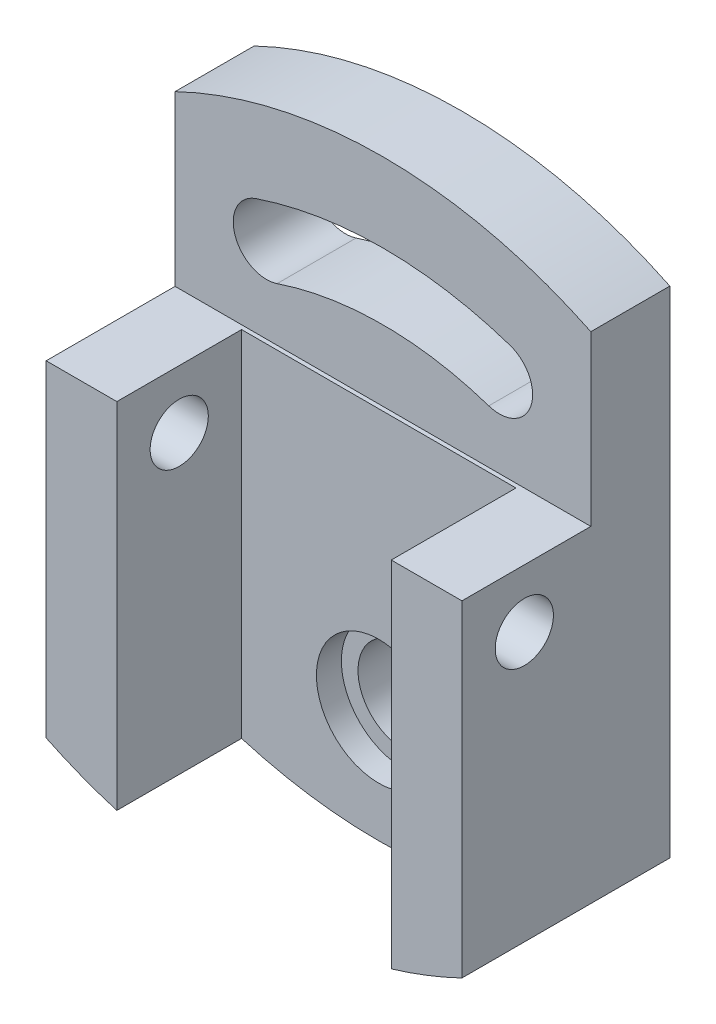
SolidWorks part; units mm, degrees
ref_plane "Front Plane" through (0, 0, 0) normal (0, 0, 1) x (1, 0, 0)
ref_plane "Top Plane" through (0, 0, 0) normal (0, 1, 0) x (1, 0, 0)
ref_plane "Right Plane" through (0, 0, 0) normal (1, 0, 0) x (0, 0, -1)
sketch "Sketch3" plane through (0, 0, 0) normal (0, 0, 1) x (1, 0, 0)
  line L0 (0, 0) -> (0, -134.0527) construction
  line L2 (-50, 103.5616) -> (-50, -15.5616)
  line L4 (50, 103.5616) -> (50, -15.5616)
  arc A0 (-50, 103.5616) -> (50, 103.5616) centre (0, 0) cw
  arc A1 (-28, 83.4266) -> (28, 83.4266) centre (0, 0) cw construction
  arc A3 (30.5455, 91.0109) -> (-30.5455, 91.0109) centre (0, 0) ccw
  arc A8 (25.4545, 75.8424) -> (-25.4545, 75.8424) centre (0, 0) ccw
  arc A9 (25.4545, 75.8424) -> (30.5455, 91.0109) centre (28, 83.4266) ccw
  arc A10 (-30.5455, 91.0109) -> (-25.4545, 75.8424) centre (-28, 83.4266) ccw
  arc A11 (-50, -15.5616) -> (50, -15.5616) centre (0, 88) ccw
  point P8 (0, 115)
  point P9 (0, 88)
  dimension "D1" = 115
  dimension "D2" = 88
  dimension "D4" = 115
  dimension "D6" = 8
  dimension "D5" = 100
  dimension "D7" = 56
extrude "Boss-Extrude1" add sketch "Sketch3" along normal blind 20
sketch "Sketch5" plane through (0, 0, 20) normal (0, 0, 1) x (1, 0, 0)
  line L0 (-50, 63) -> (-33, 63)
  line L1 (50, -15.5616) -> (50, 103.5616) construction
  line L2 (-50, 103.5616) -> (-50, -15.5616) construction
  line L3 (50, -15.5616) -> (50, 63)
  line L4 (-50, 63) -> (-50, -15.5616)
  line L5 (-33, 63) -> (-33, -22.1635)
  line L6 (33, 63) -> (33, -22.1635)
  line L7 (0, 0) -> (0, 28.0508) construction
  line L8 (33, 63) -> (50, 63)
  arc A0 (-50, -15.5616) -> (50, -15.5616) centre (0, 88) ccw construction
  arc A1 (-50, -15.5616) -> (-33, -22.1635) centre (0, 88) ccw
  arc A2 (33, -22.1635) -> (50, -15.5616) centre (0, 88) ccw
  point P5 (0, -27)
  dimension "D1" = 90
  dimension "D2" = 66
extrude "Boss-Extrude2" add sketch "Sketch5" along normal blind 30
sketch "Sketch6" plane through (0, 0, 20) normal (0, 0, 1) x (1, 0, 0)
  line L0 (-33, 63) -> (33, 63)
  line L6 (-50, 63) -> (-33, 63)
  line L7 (-33, 63) -> (-33, -22.1635)
  line L8 (33, -22.1635) -> (33, 63)
  line L9 (33, 63) -> (50, 63)
  line L10 (50, 63) -> (50, 103.5616)
  line L11 (-50, 103.5616) -> (-50, 63)
  line L12 (-50, 63) -> (-33, 63)
  line L15 (33, 63) -> (50, 63)
  line L16 (50, 63) -> (50, 103.5616)
  line L17 (-50, 103.5616) -> (-50, 63)
  arc A2 (-33, -22.1635) -> (33, -22.1635) centre (0, 88) ccw
  arc A3 (50, 103.5616) -> (-50, 103.5616) centre (0, 0) ccw
  arc A5 (50, 103.5616) -> (-50, 103.5616) centre (0, 0) ccw
  dimension "D1" = 0
extrude "Cut-Extrude1" cut sketch "Sketch6" against normal blind 1
sketch "Sketch8" plane through (0, 0, 20) normal (0, 0, 1) x (1, 0, 0)
  circle A0 centre (0, 0) radius 15
  dimension "D1" = 30
extrude "Cut-Extrude2" cut sketch "Sketch8" against normal blind 6
sketch "Sketch9" plane through (0, 0, 14) normal (0, 0, 1) x (1, 0, 0)
  circle A0 centre (0, 0) radius 11
  dimension "D1" = 22
extrude "Cut-Extrude3" cut sketch "Sketch9" against normal through all
sketch "Sketch10" plane through (50, 0, 0) normal (1, 0, 0) x (0, 0, -1)
  line L0 (-50, -15.5616) -> (-50, 63) construction
  line L1 (-50, 63) -> (-19, 63) construction
  circle A0 centre (-35, 49) radius 7
  dimension "D1" = 15
  dimension "D3" = 14
  dimension "D2" = 14
extrude "Cut-Extrude4" cut sketch "Sketch10" against normal through all
